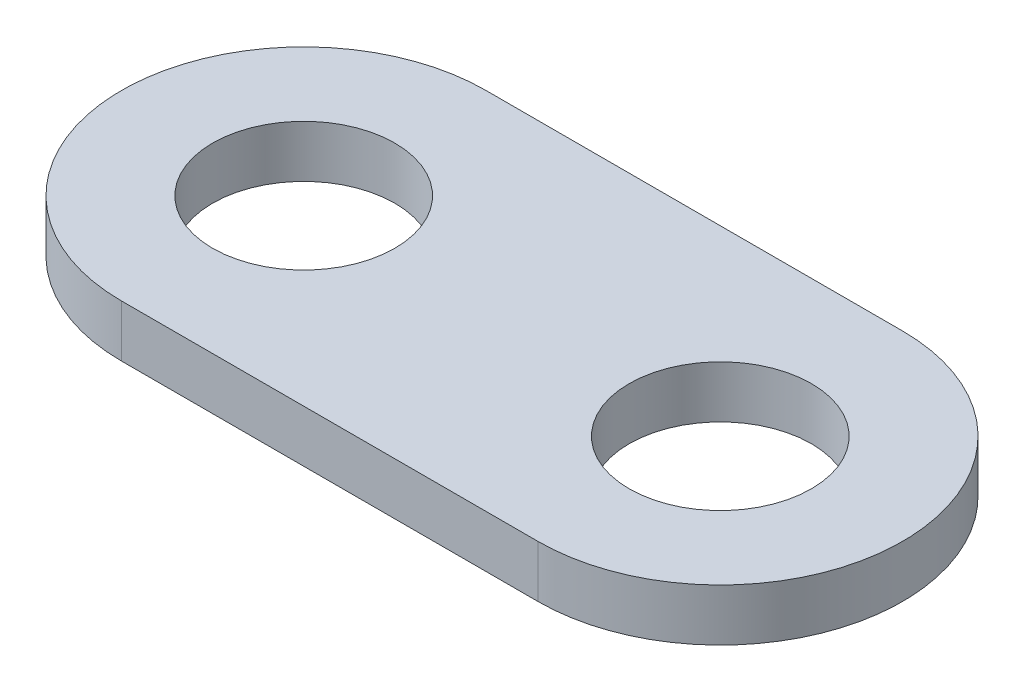
SolidWorks part; units mm, degrees
ref_plane "Front Plane" through (0, 0, 0) normal (0, 0, 1) x (1, 0, 0)
ref_plane "Top Plane" through (0, 0, 0) normal (0, 1, 0) x (1, 0, 0)
ref_plane "Right Plane" through (0, 0, 0) normal (1, 0, 0) x (0, 0, -1)
sketch "Sketch1" plane through (0, 0, 0) normal (0, 1, 0) x (1, 0, 0)
  line L0 (-93.1928, 30.7445) -> (-13.1928, 30.7445)
  line L1 (-93.1928, -39.2555) -> (-13.1928, -39.2555)
  circle A0 centre (-93.1928, -4.2555) radius 17.5
  circle A1 centre (-13.1928, -4.2555) radius 17.5
  arc A2 (-93.1928, 30.7445) -> (-93.1928, -39.2555) centre (-93.1928, -4.2555) ccw
  arc A3 (-13.1928, 30.7445) -> (-13.1928, -39.2555) centre (-13.1928, -4.2555) cw
  dimension "D1" = 35
  dimension "D2" = 35
  dimension "D3" = 80
  dimension "D4" = 35
  dimension "D5" = 35
extrude "Boss-Extrude1" add sketch "Sketch1" along normal blind 10
